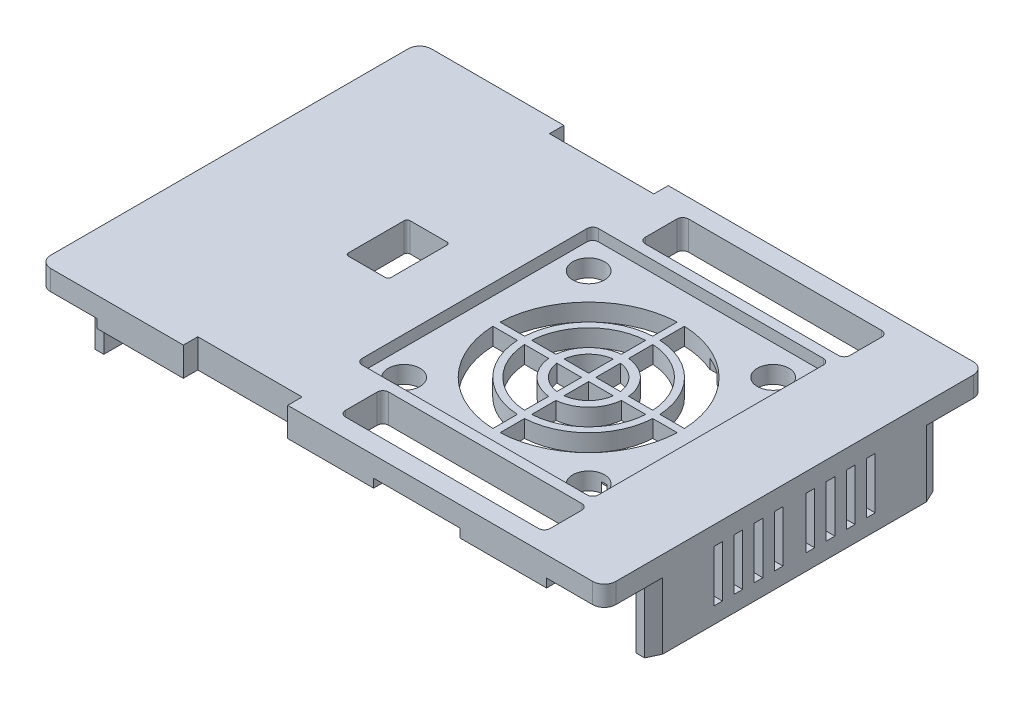
SolidWorks part; units mm, degrees
material "ABS"
ref_plane "Front Plane" through (0, 0, 0) normal (0, 0, 1) x (1, 0, 0)
ref_plane "Top Plane" through (0, 0, 0) normal (0, 1, 0) x (1, 0, 0)
ref_plane "Right Plane" through (0, 0, 0) normal (1, 0, 0) x (0, 0, -1)
sketch "Sketch1" plane through (0, 0, 0) normal (0, 1, 0) x (1, 0, 0)
  line L1 (-49, -33) -> (49, -33)
  line L2 (-49, -33) -> (-49, 33)
  line L3 (-49, 33) -> (49, 33)
  line L4 (49, -33) -> (49, 33)
  line L5 (-49, -33) -> (49, 33) construction
  line L6 (-49, 33) -> (49, -33) construction
  point P0 (0, 0)
  dimension "D1" = 98
  dimension "D2" = 66
extrude "Boss-Extrude1" add sketch "Sketch1" along normal blind 5
sketch "Sketch2" plane through (0, 0, 0) normal (0, -1, 0) x (1, 0, 0)
  line L0 (-39, 33) -> (-39, 30.5)
  line L1 (-46.5, -30.5) -> (-39, -30.5)
  line L2 (-46.5, -30.5) -> (-46.5, -24.3)
  line L3 (-46.5, 30.5) -> (-39, 30.5)
  line L4 (46.5, -30.5) -> (46.5, -25)
  line L5 (-46.5, -30.5) -> (46.5, 30.5) construction
  line L6 (-46.5, 30.5) -> (46.5, -30.5) construction
  line L7 (-24, 33) -> (-24, 30.5)
  line L8 (-5.9, 33) -> (-5.9, 30.5)
  line L9 (9, 33) -> (9, 30.5)
  line L10 (49, -33) -> (49, 33)
  line L11 (49, 33) -> (-49, 33)
  line L12 (-49, 33) -> (-49, -33)
  line L13 (-49, -33) -> (49, -33)
  line L14 (49, -33) -> (49, -25)
  line L15 (49, 33) -> (39, 33)
  line L16 (-49, 33) -> (-49, 24.3)
  line L17 (-49, -33) -> (-39, -33)
  line L18 (24, 33) -> (24, 30.5)
  line L19 (39, 33) -> (39, 30.5)
  line L20 (2.75, 0) -> (-2.75, 0) construction
  line L21 (39, -33) -> (39, -30.5)
  line L22 (24, -33) -> (24, -30.5)
  line L23 (9, -33) -> (9, -30.5)
  line L24 (-5.9, -33) -> (-5.9, -30.5)
  line L25 (-24, -33) -> (-24, -30.5)
  line L27 (-39, -33) -> (-39, -30.5)
  line L28 (-49, 24.3) -> (-46.5, 24.3)
  line L29 (-49, -24.3) -> (-46.5, -24.3)
  line L30 (46.5, 25) -> (49, 25)
  line L31 (46.5, -25) -> (49, -25)
  line L32 (-49, -24.3) -> (-49, -33)
  line L33 (-46.5, 24.3) -> (-46.5, 30.5)
  line L34 (-24, 30.5) -> (-5.9, 30.5)
  line L35 (-39, 33) -> (-49, 33)
  line L36 (9, 30.5) -> (24, 30.5)
  line L37 (-5.9, 33) -> (-24, 33)
  line L38 (24, 33) -> (9, 33)
  line L39 (39, 30.5) -> (46.5, 30.5)
  line L40 (46.5, 25) -> (46.5, 30.5)
  line L41 (49, 25) -> (49, 33)
  line L42 (39, -30.5) -> (46.5, -30.5)
  line L44 (39, -33) -> (49, -33)
  line L45 (9, -33) -> (24, -33)
  line L46 (9, -30.5) -> (24, -30.5)
  line L48 (-24, -30.5) -> (-5.9, -30.5)
  line L50 (-24, -33) -> (-5.9, -33)
  point P0 (0, 0)
  point P22 (9, 31.75)
  point P23 (24, 31.75)
  dimension "D1" = 61
  dimension "D2" = 93
  dimension "D4" = 7.5
  dimension "D5" = 15
  dimension "D7" = 14.9
  dimension "D8" = 15
  dimension "D9" = 15
  dimension "D10" = 6.2
  dimension "D11" = 6.2
  dimension "D12" = 5.5
  dimension "D13" = 5.5
  dimension "D14" = 10
  dimension "D3" = 0
extrude "Cut-Extrude1" cut sketch "Sketch2" against normal blind 1.5
fillet "Fillet1" radius 2 4 edges at (49, 3.25, -33) (49, 3.25, 33) (-49, 3.25, -33) (-49, 3.25, 33)
sketch "Sketch3" plane through (0, 5, 0) normal (0, 1, 0) x (1, 0, 0)
  line L0 (-2.75, 0) -> (2.75, 0) construction
  line L1 (49, -31) -> (49, 31) construction
  line L2 (-5.5, -20.5) -> (33.5, -20.5)
  line L3 (-6.5, -19.5) -> (-6.5, 19.5)
  line L4 (-5.5, 20.5) -> (33.5, 20.5)
  line L5 (34.5, -19.5) -> (34.5, 19.5)
  line L6 (-6.5, -20.5) -> (34.5, 20.5) construction
  line L7 (-6.5, 20.5) -> (34.5, -20.5) construction
  arc A0 (33.5, -20.5) -> (34.5, -19.5) centre (33.5, -19.5) ccw
  arc A1 (-5.5, -20.5) -> (-6.5, -19.5) centre (-5.5, -19.5) cw
  arc A2 (-6.5, 19.5) -> (-5.5, 20.5) centre (-5.5, 19.5) cw
  arc A3 (33.5, 20.5) -> (34.5, 19.5) centre (33.5, 19.5) cw
  point P2 (14, 0)
  dimension "D4" = 1
  dimension "D1" = 41
  dimension "D2" = 41
  dimension "D3" = 35
extrude "Cut-Extrude2" cut sketch "Sketch3" against normal blind 2
sketch "Sketch4" plane through (0, 3, 0) normal (0, 1, 0) x (1, 0, 0)
  line L0 (13.375, 5.6038) -> (13.375, 9.803)
  line L1 (14.625, 11.0379) -> (14.625, 15.2813)
  line L2 (13.375, 11.0379) -> (13.375, 15.2813)
  line L3 (20.3105, -0.083) -> (24.5096, -0.083)
  line L4 (3.4904, -0.083) -> (7.6895, -0.083)
  line L5 (14.625, -0.0815) -> (30, 15.2935) construction
  line L6 (25.7445, -0.083) -> (29.9878, -0.083)
  line L11 (-2, -16.7065) -> (13.375, -1.3315) construction
  line L12 (-2, 15.2935) -> (13.375, -0.0815) construction
  line L14 (13.375, -3.295) -> (13.375, -1.3301)
  line L16 (14.625, -3.295) -> (14.625, -1.3301)
  line L17 (20.3105, -1.3301) -> (24.5096, -1.3301)
  line L18 (14.625, -0.083) -> (18.894, -0.083)
  line L21 (14.625, -1.3301) -> (18.894, -1.3301)
  line L23 (25.7445, -1.3301) -> (29.9878, -1.3301)
  line L24 (14, -0.083) -> (14, -0.0851) construction
  line L26 (13.375, -16.6943) -> (13.375, -12.4509)
  line L28 (14.625, -16.6943) -> (14.625, -12.4509)
  line L31 (-1.9878, -0.083) -> (2.2555, -0.083)
  line L33 (-1.9878, -1.3301) -> (2.2555, -1.3301)
  line L35 (3.4904, -1.3301) -> (7.6895, -1.3301)
  line L36 (9.106, -0.083) -> (13.375, -0.083)
  line L38 (9.106, -1.3301) -> (13.375, -1.3301)
  line L39 (13.375, -11.2161) -> (13.375, -7.0169)
  line L40 (14.625, -11.2161) -> (14.625, -7.0169)
  line L41 (13.375, -5.6004) -> (13.375, -1.3301)
  line L42 (14.625, -5.6004) -> (14.625, -1.3301)
  line L44 (14.625, -1.3315) -> (30, -16.7065) construction
  line L45 (14.625, 5.6038) -> (14.625, 9.803)
  line L47 (14, -1.328) -> (14, -1.3301) construction
  line L50 (13.375, -0.083) -> (13.375, 4.1873)
  line L51 (13.375, -0.083) -> (13.375, 1.4139)
  line L57 (14.625, -0.083) -> (14.625, 4.1873)
  line L58 (14.625, -0.083) -> (14.625, 1.4139)
  circle A0 centre (30, 15.2935) radius 2.75
  circle A1 centre (30, -16.7065) radius 2.75
  circle A2 centre (-2, -16.7065) radius 2.75
  circle A3 centre (-2, 15.2935) radius 2.75
  circle A5 centre (14, -0.7065) radius 17.25
  arc A6 (-1.9878, -1.3301) -> (13.375, -16.6943) centre (14, -0.7065) ccw
  arc A7 (2.2555, -1.3301) -> (13.375, -12.4509) centre (14, -0.7065) ccw
  arc A8 (3.4904, -1.3301) -> (13.375, -11.2161) centre (14, -0.7065) ccw
  arc A9 (9.106, -1.3301) -> (13.375, -5.6004) centre (14, -0.7065) ccw
  arc A10 (7.6895, -1.3301) -> (13.375, -7.0169) centre (14, -0.7065) ccw
  arc A11 (14.625, -16.6943) -> (29.9878, -1.3301) centre (14, -0.7065) ccw
  arc A12 (14.625, -12.4509) -> (25.7445, -1.3301) centre (14, -0.7065) ccw
  arc A13 (14.625, -11.2161) -> (24.5096, -1.3301) centre (14, -0.7065) ccw
  arc A14 (14.625, -7.0169) -> (20.3105, -1.3301) centre (14, -0.7065) ccw
  arc A15 (14.625, -5.6004) -> (18.894, -1.3301) centre (14, -0.7065) ccw
  arc A16 (18.894, -0.083) -> (14.625, 4.1873) centre (14, -0.7065) ccw
  arc A17 (20.3105, -0.083) -> (14.625, 5.6038) centre (14, -0.7065) ccw
  arc A18 (24.5096, -0.083) -> (14.625, 9.803) centre (14, -0.7065) ccw
  arc A19 (29.9878, -0.083) -> (14.625, 15.2813) centre (14, -0.7065) ccw
  arc A20 (25.7445, -0.083) -> (14.625, 11.0379) centre (14, -0.7065) ccw
  arc A21 (13.375, 4.1873) -> (9.106, -0.083) centre (14, -0.7065) ccw
  arc A22 (13.375, 5.6038) -> (7.6895, -0.083) centre (14, -0.7065) ccw
  arc A23 (13.375, 9.803) -> (3.4904, -0.083) centre (14, -0.7065) ccw
  arc A24 (13.375, 11.0379) -> (2.2555, -0.083) centre (14, -0.7065) ccw
  arc A26 (13.375, 15.2813) -> (-1.9878, -0.083) centre (14, -0.7065) ccw
  point P12 (14, -0.7065)
  point P30 (0, 0)
  point P31 (14, 7.4864)
  point P36 (24.5281, -0.7065)
  point P41 (14, -9.299)
  point P46 (0.4907, -0.7065)
  point P48 (0, 0)
  dimension "D3" = 5.5
  dimension "D5" = 1.4077
  dimension "D1" = 32
  dimension "D2" = 32
  dimension "1.25" = 1.25
  dimension "D4" = 4
extrude "Cut-Extrude3" cut sketch "Sketch4" against normal up to next contours L21 A15 L42 | L17 A13 L40 A14 | L45 A18 L3 A17 | L6 A19 L1 A20 | A11 L23 A12 L28 | L26 A7 L33 A6 | L39 A10 L35 A8 | L41 A9 L38 | L18 A16 L57 | L50 A21 L36 | L0 A23 L4 A22 | A26 L31 A24 L2 | A2 | A3 | A0 | A1
sketch "Sketch5" plane through (0, 5, 0) normal (0, 1, 0) x (1, 0, 0)
  line L0 (32.0607, -20.5) -> (32.0607, 20.5) construction
  line L1 (-16.6417, -5.3404) -> (-23.032, -5.3404)
  line L2 (-16.1417, -4.8404) -> (-16.1417, 4.8404)
  line L3 (-16.6417, 5.3404) -> (-23.032, 5.3404)
  line L4 (-23.532, -4.8404) -> (-23.532, 4.8404)
  line L5 (-16.1417, -5.3404) -> (-23.532, 5.3404) construction
  line L6 (-16.1417, 5.3404) -> (-23.532, -5.3404) construction
  line L7 (-5.5, -20.5) -> (33.5, -20.5) construction
  line L8 (33.5, 20.5) -> (-5.5, 20.5) construction
  line L9 (32.0607, 0) -> (-11.7503, 0) construction
  line L10 (-4.7258, 20.5) -> (-4.7258, -20.5) construction
  arc A0 (-23.032, -5.3404) -> (-23.532, -4.8404) centre (-23.032, -4.8404) cw
  arc A1 (-16.6417, -5.3404) -> (-16.1417, -4.8404) centre (-16.6417, -4.8404) ccw
  arc A2 (-16.1417, 4.8404) -> (-16.6417, 5.3404) centre (-16.6417, 4.8404) ccw
  arc A3 (-23.032, 5.3404) -> (-23.532, 4.8404) centre (-23.032, 4.8404) ccw
  point P0 (-19.8368, 0)
  point P26 (-19.8368, 0)
  dimension "D1" = 0.5
extrude "Cut-Extrude4" cut sketch "Sketch5" against normal up to next
chamfer "Chamfer1" distance 1 angle 65 4 edges at (-49, 0.75, -24.3) (49, 0.75, 25) (49, 0.75, -25) (-49, 0.75, 24.3)
sketch "Sketch6" plane through (0, 0, 0) normal (0, -1, 0) x (1, 0, 0)
  line L0 (-46.5, -24.3) -> (-46.5, 24.3) construction
  line L1 (-46.5, -30.5) -> (-46.5, -24.3) construction
  line L2 (-46.5, 24.3) -> (-46.5, 2.3)
  line L3 (-46.5, 2.3) -> (-49, 2.3)
  line L4 (-49, -22.1555) -> (-49, 22.1555) construction
  line L5 (-49, 2.3) -> (-49, 22.1555)
  line L6 (-49, 22.1555) -> (-48, 24.3)
  line L7 (-48, 24.3) -> (-46.5, 24.3)
  dimension "D1" = 22
extrude "Boss-Extrude2" add sketch "Sketch6" along normal blind 12
fillet "Fillet2" radius 1 1 edges at (-49, -6, 2.3)
sketch "Sketch7" plane through (0, 0, 0) normal (0, -1, 0) x (1, 0, 0)
  line L0 (46.5, 25) -> (46.5, -25)
  line L1 (46.5, -25) -> (48, -25)
  line L2 (48, -25) -> (49, -22.8555)
  line L3 (49, -22.8555) -> (49, 22.8555)
  line L4 (49, 22.8555) -> (48, 25)
  line L5 (49, 22.8555) -> (48, 25) construction
  line L6 (46.5, 25) -> (48, 25) construction
  line L7 (48, 25) -> (46.5, 25)
extrude "Boss-Extrude3" add sketch "Sketch7" along normal blind 10
sketch "Sketch8" plane through (49, 0, 0) normal (1, 0, 0) x (0, 0, -1)
  line L0 (0, 5) -> (0, -10) construction
  line L1 (-31, 5) -> (31, 5) construction
  line L2 (22.8555, -10) -> (-22.8555, -10) construction
  line L3 (-8, 5) -> (-8, -10) construction
  line L4 (-3.5, 1.7311) -> (-2, 1.7311)
  line L5 (-3.5, 1.7311) -> (-3.5, -7.2)
  line L6 (-3.5, -7.2) -> (-2, -7.2)
  line L7 (-2, 1.7311) -> (-2, -7.2)
  line L8 (-5.5, 1.7311) -> (-7, 1.7311)
  line L9 (-5.5, 1.7311) -> (-5.5, -7.2)
  line L10 (-5.5, -7.2) -> (-7, -7.2)
  line L11 (-7, 1.7311) -> (-7, -7.2)
  line L12 (-12.5, -7.2) -> (-14, -7.2)
  line L13 (-14, 1.7311) -> (-14, -7.2)
  line L14 (-12.5, 1.7311) -> (-14, 1.7311)
  line L15 (-12.5, 1.7311) -> (-12.5, -7.2)
  line L16 (-10.5, -7.2) -> (-9, -7.2)
  line L17 (-9, 1.7311) -> (-9, -7.2)
  line L18 (-10.5, 1.7311) -> (-9, 1.7311)
  line L19 (-10.5, 1.7311) -> (-10.5, -7.2)
  line L20 (3.5, -7.2) -> (2, -7.2)
  line L21 (2, 1.7311) -> (2, -7.2)
  line L22 (3.5, 1.7311) -> (2, 1.7311)
  line L23 (3.5, 1.7311) -> (3.5, -7.2)
  line L24 (5.5, -7.2) -> (7, -7.2)
  line L25 (7, 1.7311) -> (7, -7.2)
  line L26 (5.5, 1.7311) -> (7, 1.7311)
  line L27 (5.5, 1.7311) -> (5.5, -7.2)
  line L28 (10.5, 1.7311) -> (10.5, -7.2)
  line L29 (10.5, 1.7311) -> (9, 1.7311)
  line L30 (9, 1.7311) -> (9, -7.2)
  line L31 (10.5, -7.2) -> (9, -7.2)
  line L32 (12.5, 1.7311) -> (12.5, -7.2)
  line L33 (12.5, 1.7311) -> (14, 1.7311)
  line L34 (14, 1.7311) -> (14, -7.2)
  line L35 (12.5, -7.2) -> (14, -7.2)
  dimension "D1" = 2
  dimension "D2" = 2
  dimension "D3" = 1.5
  dimension "D4" = 1.5
  dimension "D5" = 1
  dimension "D6" = 2.8
  dimension "D7" = 2.8
extrude "Cut-Extrude5" cut sketch "Sketch8" against normal up to next
sketch "Sketch9" plane through (0, 5, 0) normal (0, 1, 0) x (1, 0, 0)
  line L0 (-9.35, 0) -> (9.35, 0) construction
  line L3 (3.6118, 33) -> (3.6118, -33) construction
  line L4 (47, 33) -> (-47, 33) construction
  line L5 (-47, -33) -> (47, -33) construction
  line L6 (3.6118, -26) -> (31.6118, -26) construction
  line L7 (3.6118, -22.25) -> (31.6118, -22.25)
  line L8 (3.6118, -29.75) -> (31.6118, -29.75)
  line L9 (3.6118, -22.25) -> (0.8618, -22.25)
  line L11 (3.6118, -29.75) -> (0.8618, -29.75)
  line L13 (-0.1382, -23.25) -> (-0.1382, -28.75)
  line L14 (35.3618, -26) -> (35.3618, -23.25)
  line L15 (31.6118, -22.25) -> (34.3618, -22.25)
  line L16 (35.3618, -26) -> (35.3618, -28.75)
  line L17 (31.6118, -29.75) -> (34.3618, -29.75)
  line L18 (3.6118, 26) -> (31.6118, 26) construction
  line L19 (31.6118, 29.75) -> (34.3618, 29.75)
  line L20 (35.3618, 26) -> (35.3618, 28.75)
  line L21 (31.6118, 22.25) -> (34.3618, 22.25)
  line L22 (35.3618, 26) -> (35.3618, 23.25)
  line L23 (-0.1382, 23.25) -> (-0.1382, 28.75)
  line L24 (3.6118, 29.75) -> (0.8618, 29.75)
  line L25 (3.6118, 22.25) -> (0.8618, 22.25)
  line L26 (3.6118, 29.75) -> (31.6118, 29.75)
  line L27 (3.6118, 22.25) -> (31.6118, 22.25)
  arc A2 (34.3618, -29.75) -> (35.3618, -28.75) centre (34.3618, -28.75) ccw
  arc A3 (0.8618, -29.75) -> (-0.1382, -28.75) centre (0.8618, -28.75) cw
  arc A4 (-0.1382, -23.25) -> (0.8618, -22.25) centre (0.8618, -23.25) cw
  arc A5 (34.3618, -22.25) -> (35.3618, -23.25) centre (34.3618, -23.25) cw
  arc A6 (34.3618, 29.75) -> (35.3618, 28.75) centre (34.3618, 28.75) cw
  arc A7 (34.3618, 22.25) -> (35.3618, 23.25) centre (34.3618, 23.25) ccw
  arc A8 (-0.1382, 23.25) -> (0.8618, 22.25) centre (0.8618, 23.25) ccw
  arc A9 (-0.1382, 28.75) -> (0.8618, 29.75) centre (0.8618, 28.75) cw
  point P13 (17.6118, -26)
  point P22 (0, 0)
  point P27 (0, 0)
  point P33 (17.6118, 26)
  point P36 (35.3618, -29.75)
  point P39 (-0.1382, -29.75)
  point P42 (-0.1382, -22.25)
  point P45 (35.3618, -22.25)
  point P48 (35.3618, 29.75)
  point P51 (35.3618, 22.25)
  point P54 (-0.1382, 22.25)
  point P57 (-0.1382, 29.75)
  dimension "D1" = 1
  dimension "D2" = 7.5
  dimension "D3" = 28
  dimension "D5" = 7
extrude "Cut-Extrude6" cut sketch "Sketch9" against normal up to next
sketch "Sketch10" plane through (-49, 0, 0) normal (-1, 0, 0) x (0, 0, 1)
  line L0 (3.3, 0) -> (22.1555, 0) construction
  line L1 (22.1555, -12) -> (22.1555, 1.5) construction
  line L2 (12.7277, 0) -> (12.7277, -1.5) construction
  line L3 (22.1555, -12) -> (3.3, -12) construction
  line L4 (10.4777, -10.5) -> (8.9777, -10.5)
  line L5 (11.9777, -1.5) -> (13.4777, -1.5)
  line L7 (11.9777, -10.5) -> (13.4777, -10.5)
  line L8 (13.4777, -1.5) -> (13.4777, -10.5)
  line L9 (14.9777, -1.5) -> (16.4777, -1.5)
  line L10 (14.9777, -1.5) -> (14.9777, -10.5)
  line L11 (14.9777, -10.5) -> (16.4777, -10.5)
  line L12 (16.4777, -1.5) -> (16.4777, -10.5)
  line L13 (8.9777, -1.5) -> (8.9777, -10.5)
  line L14 (10.4777, -1.5) -> (8.9777, -1.5)
  line L15 (10.4777, -1.5) -> (10.4777, -10.5)
  line L16 (11.9777, -1.5) -> (11.9777, -10.5)
  line L17 (12.7277, -10.5) -> (12.7277, -12) construction
  dimension "D1" = 0.75
  dimension "D2" = 1.5
  dimension "D3" = 1.5
  dimension "D4" = 1.5
  dimension "D5" = 1.5
  dimension "D6" = 1.5
  dimension "D7" = 1.5
extrude "Cut-Extrude7" cut sketch "Sketch10" against normal up to next
sketch "Sketch13" plane through (0, 1.5, 0) normal (0, -1, 0) x (1, 0, 0)
  line L4 (-5.9, 33) -> (-24, 33)
  line L5 (-24, 33) -> (-24, 30.5)
  line L6 (-24, 30.5) -> (-5.9, 30.5)
  line L7 (-5.9, 30.5) -> (-5.9, 33)
  line L8 (-5.9, 33) -> (-24, 33)
  line L9 (-24, 33) -> (-24, 30.5)
  line L10 (-24, 30.5) -> (-5.9, 30.5)
  line L11 (-5.9, 30.5) -> (-5.9, 33)
  dimension "D1" = 0
extrude "Cut-Extrude9" cut sketch "Sketch13" against normal up to next (3.5 mm away)
mirror "Mirror1" about plane through (0, 0, 0) normal (0, 0, 1) of "Cut-Extrude9"
